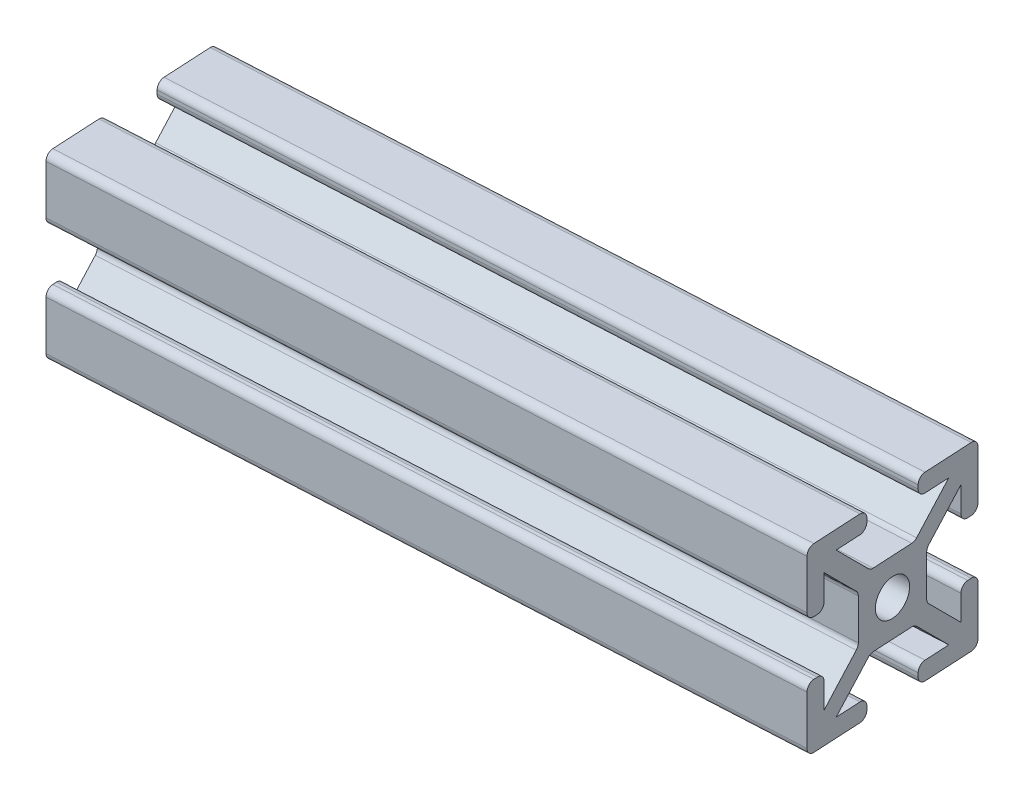
SolidWorks part; units mm, degrees
material "1060 Alloy"
ref_plane "Front Plane" through (0, 0, 0) normal (0, 0, 1) x (1, 0, 0)
ref_plane "Top Plane" through (0, 0, 0) normal (0, 1, 0) x (1, 0, 0)
ref_plane "Right Plane" through (0, 0, 0) normal (1, 0, 0) x (0, 0, -1)
sketch "Sketch1" plane through (0, 0, 0) normal (0, 1, 0) x (1, 0, 0)
  line L0 (0, 0) -> (79.8868, 4.2537)
other "Size 4X4 (1)"
ref_plane "Plane1" through (0, 0, 0) normal (0.9986, 0, -0.0532) x (-0.0532, 0, -0.9986)
sketch "Sketch11" plane through (0, 0, 0) normal (0.9986, 0, -0.0532) x (-0.0532, 0, -0.9986)
  line L0 (-3, 9.2) -> (-3, 8.8)
  line L1 (-2.2544, 4) -> (2.2544, 4)
  line L2 (-4, 2.2544) -> (-4, -2.2544)
  line L3 (-2.2544, -4) -> (2.2544, -4)
  line L4 (4, 2.2544) -> (4, -2.2544)
  line L7 (-6.5858, 8) -> (-3.8, 8)
  line L8 (-8, 6.5858) -> (-8, 3.8)
  line L9 (-6.5858, -8) -> (-3.8, -8)
  line L10 (8, 6.5858) -> (8, 3.8)
  line L12 (9.7657, -9.7657) -> (10, -10) construction
  line L13 (-9.2, 10) -> (-3.8, 10)
  line L14 (-10, 9.2) -> (-10, 3.8)
  line L15 (-9.2, -10) -> (-3.8, -10)
  line L16 (10, 9.2) -> (10, 3.8)
  line L17 (-10, 10) -> (-9.7657, 9.7657) construction
  line L18 (-10, -10) -> (-9.7657, -9.7657) construction
  line L21 (3, 9.2) -> (3, 8.8)
  line L22 (3, -9.2) -> (3, -8.8)
  line L23 (-3, -9.2) -> (-3, -8.8)
  line L24 (3.8, 10) -> (9.2, 10)
  line L25 (3.8, 8) -> (6.5858, 8)
  line L26 (-9.2, 3) -> (-8.8, 3)
  line L27 (9.2, 3) -> (8.8, 3)
  line L28 (9.2, -3) -> (8.8, -3)
  line L29 (-9.2, -3) -> (-8.8, -3)
  line L30 (-10, -3.8) -> (-10, -9.2)
  line L31 (-8, -3.8) -> (-8, -6.5858)
  line L32 (8, -3.8) -> (8, -6.5858)
  line L33 (10, -3.8) -> (10, -9.2)
  line L34 (3.8, -8) -> (6.5858, -8)
  line L35 (3.8, -10) -> (9.2, -10)
  line L36 (6.5858, 8) -> (2.8201, 4.2343)
  line L37 (8, 6.5858) -> (4.2343, 2.8201)
  line L38 (8, -6.5858) -> (4.2343, -2.8201)
  line L39 (6.5858, -8) -> (2.8201, -4.2343)
  line L40 (-6.5858, -8) -> (-2.8201, -4.2343)
  line L41 (-8, -6.5858) -> (-4.2343, -2.8201)
  line L42 (-8, 6.5858) -> (-4.2343, 2.8201)
  line L43 (-6.5858, 8) -> (-2.8201, 4.2343)
  line L47 (9.7657, 9.7657) -> (10, 10) construction
  circle A0 centre (0, 0) radius 2
  arc A1 (9.2, -3) -> (10, -3.8) centre (9.2, -3.8) cw
  arc A2 (8.8, -3) -> (8, -3.8) centre (8.8, -3.8) ccw
  arc A3 (3, -9.2) -> (3.8, -10) centre (3.8, -9.2) ccw
  arc A4 (3, -8.8) -> (3.8, -8) centre (3.8, -8.8) cw
  arc A5 (-3, -9.2) -> (-3.8, -10) centre (-3.8, -9.2) cw
  arc A6 (-3, -8.8) -> (-3.8, -8) centre (-3.8, -8.8) ccw
  arc A7 (-8.8, -3) -> (-8, -3.8) centre (-8.8, -3.8) cw
  arc A8 (-9.2, -3) -> (-10, -3.8) centre (-9.2, -3.8) ccw
  arc A9 (-10, -9.2) -> (-9.2, -10) centre (-9.2, -9.2) ccw
  arc A10 (9.2, -10) -> (10, -9.2) centre (9.2, -9.2) ccw
  arc A11 (9.2, 10) -> (10, 9.2) centre (9.2, 9.2) cw
  arc A12 (-9.2, 10) -> (-10, 9.2) centre (-9.2, 9.2) ccw
  arc A13 (9.2, 3) -> (10, 3.8) centre (9.2, 3.8) ccw
  arc A14 (8.8, 3) -> (8, 3.8) centre (8.8, 3.8) cw
  arc A15 (3, 9.2) -> (3.8, 10) centre (3.8, 9.2) cw
  arc A16 (3, 8.8) -> (3.8, 8) centre (3.8, 8.8) ccw
  arc A17 (-3, 9.2) -> (-3.8, 10) centre (-3.8, 9.2) ccw
  arc A18 (-3, 8.8) -> (-3.8, 8) centre (-3.8, 8.8) cw
  arc A19 (-8.8, 3) -> (-8, 3.8) centre (-8.8, 3.8) ccw
  arc A20 (-9.2, 3) -> (-10, 3.8) centre (-9.2, 3.8) cw
  arc A21 (-2.8201, 4.2343) -> (-2.2544, 4) centre (-2.2544, 4.8) ccw
  arc A22 (4.2343, 2.8201) -> (4, 2.2544) centre (4.8, 2.2544) ccw
  arc A23 (2.8201, 4.2343) -> (2.2544, 4) centre (2.2544, 4.8) cw
  arc A24 (4.2343, -2.8201) -> (4, -2.2544) centre (4.8, -2.2544) cw
  arc A25 (2.8201, -4.2343) -> (2.2544, -4) centre (2.2544, -4.8) ccw
  arc A26 (-2.8201, -4.2343) -> (-2.2544, -4) centre (-2.2544, -4.8) cw
  arc A27 (-4.2343, -2.8201) -> (-4, -2.2544) centre (-4.8, -2.2544) ccw
  arc A28 (-4.2343, 2.8201) -> (-4, 2.2544) centre (-4.8, 2.2544) cw
  point P7 (0, 0)
  point P10 (-2.5858, 4)
  point P53 (10, -3)
  point P56 (8, -3)
  point P59 (3, -10)
  point P62 (3, -8)
  point P65 (-3, -10)
  point P68 (-3, -8)
  point P71 (-8, -3)
  point P74 (-10, -3)
  point P89 (10, 3)
  point P92 (8, 3)
  point P95 (3, 10)
  point P98 (3, 8)
  point P101 (-3, 10)
  point P104 (-3, 8)
  point P107 (-8, 3)
  point P110 (-10, 3)
  point P116 (4, 2.5858)
  point P119 (2.5858, 4)
  point P122 (4, -2.5858)
  point P125 (2.5858, -4)
  point P128 (-2.5858, -4)
  point P131 (-4, -2.5858)
  point P134 (-4, 2.5858)
  dimension "D3" = 4
  dimension "D11" = 0.8
  dimension "D12" = 0.8
  dimension "D2" = 0.8
  dimension "D4" = 20
  dimension "D6" = 20
  dimension "D8" = 7
  dimension "D9" = 7
